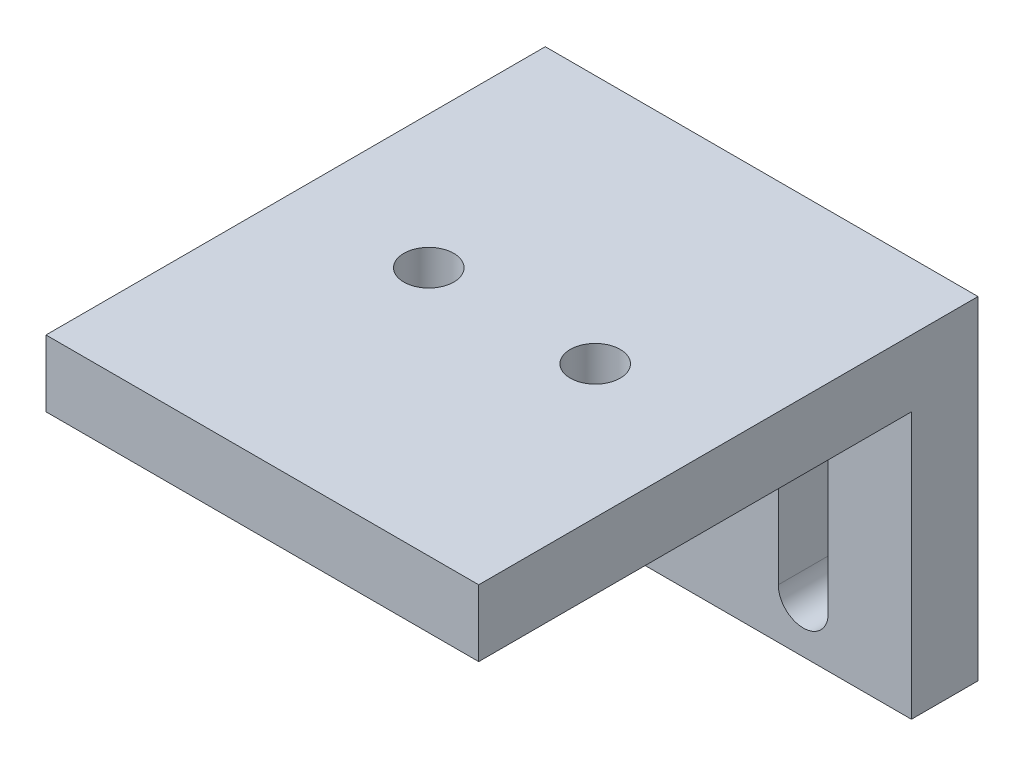
SolidWorks part; units mm, degrees
ref_plane "Front Plane" through (0, 0, 0) normal (0, 0, 1) x (1, 0, 0)
ref_plane "Top Plane" through (0, 0, 0) normal (0, 1, 0) x (1, 0, 0)
ref_plane "Right Plane" through (0, 0, 0) normal (1, 0, 0) x (0, 0, -1)
sketch "Croquis1" plane through (0, 0, 0) normal (0, 1, 0) x (1, 0, 0)
  line L0 (-13, -2) -> (-13, 2)
  line L1 (-13, -2) -> (13, -2)
  line L2 (-13, 2) -> (13, 2)
  line L3 (13, -2) -> (13, 2)
  line L4 (-13, -2) -> (13, 2) construction
  line L5 (-13, 2) -> (13, -2) construction
  point P1 (0, 0)
  dimension "D1" = 4
  dimension "D2" = 26
extrude "Saliente-Extruir1" add sketch "Croquis1" along normal blind 20
sketch "Croquis2" plane through (0, 0, 2) normal (0, 0, 1) x (1, 0, 0)
  line L0 (-13, 16) -> (-13, 20)
  line L1 (-13, 16) -> (13, 16)
  line L2 (-13, 20) -> (13, 20)
  line L3 (13, 16) -> (13, 20)
  line L4 (-13, 16) -> (13, 20) construction
  line L5 (-13, 20) -> (13, 16) construction
  line L6 (-13, 0) -> (13, 0) construction
  point P1 (0, 18)
  dimension "D1" = 4
  dimension "D2" = 26
  dimension "D3" = 16
extrude "Saliente-Extruir2" add sketch "Croquis2" along normal blind 26
sketch "Croquis3" plane through (0, 20, 0) normal (0, 1, 0) x (1, 0, 0)
  line L0 (-13, 2) -> (-13, -28) construction
  line L2 (13, 2) -> (-13, 2) construction
  circle A0 centre (-5, -13) radius 1.5
  circle A1 centre (5, -13) radius 1.5
  dimension "D4" = 3
  dimension "D5" = 3
  dimension "D1" = 10
  dimension "D2" = 8
  dimension "D3" = 15
  dimension "D6" = 15
extrude "Cortar-Extruir1" cut sketch "Croquis3" against normal blind 25
sketch "Croquis4" plane through (0, 0, 2) normal (0, 0, 1) x (1, 0, 0)
  line L0 (0, 0) -> (0, 18.7593) construction
  line L1 (-13, 0) -> (13, 0) construction
  line L2 (-13, 8) -> (0, 8) construction
  line L3 (-13, 16) -> (-13, 0) construction
  line L4 (0, 8) -> (13, 8) construction
  line L5 (13, 16) -> (13, 0) construction
  line L6 (-6.5, 13) -> (-6.5, 3) construction
  line L7 (-8, 13) -> (-8, 3)
  line L8 (-5, 13) -> (-5, 3)
  line L9 (5, 13) -> (5, 3)
  line L10 (8, 13) -> (8, 3)
  arc A0 (-5, 13) -> (-8, 13) centre (-6.5, 13) ccw
  arc A1 (-5, 3) -> (-8, 3) centre (-6.5, 3) cw
  arc A2 (5, 3) -> (8, 3) centre (6.5, 3) ccw
  arc A3 (5, 13) -> (8, 13) centre (6.5, 13) cw
  point P13 (-6.5, 8)
  point P19 (-5, 8)
  point P20 (-8, 8)
  dimension "D2" = 3
  dimension "D1" = 10
extrude "Cortar-Extruir2" cut sketch "Croquis4" against normal blind 25
